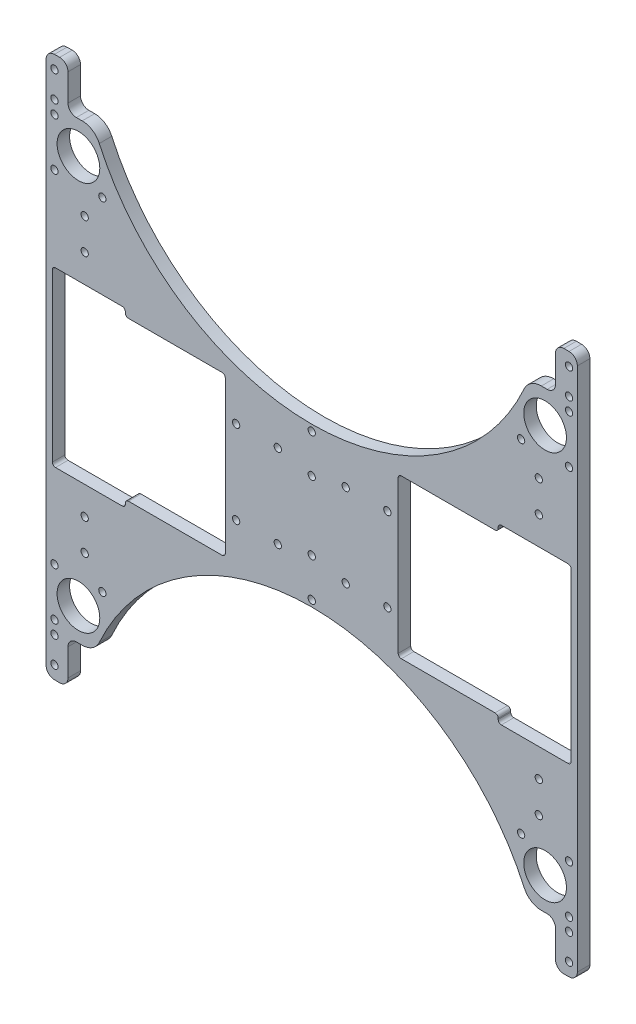
SolidWorks part; units mm, degrees
ref_plane "Plan de face" through (0, 0, 0) normal (0, 0, 1) x (1, 0, 0)
ref_plane "Plan de dessus" through (0, 0, 0) normal (0, 1, 0) x (1, 0, 0)
ref_plane "Plan de droite" through (0, 0, 0) normal (1, 0, 0) x (0, 0, -1)
sketch "Esquisse1" plane through (0, 0, 0) normal (0, 0, 1) x (1, 0, 0)
  line L0 (-109, -55) -> (-109, 55) construction
  line L1 (-16.3, -20) -> (-36.3, -20) construction
  line L2 (-16.3, -20) -> (-16.3, 20) construction
  line L5 (-16.3, 20) -> (-36.3, 20) construction
  line L7 (-36.3, -20) -> (-36.3, 20) construction
  line L8 (-5, 0) -> (-85.5, 0) construction
  line L11 (-41.5, 23) -> (-85.5, 23) construction
  line L13 (-41.5, 38) -> (-89.5, 38)
  line L14 (-41.5, 38) -> (-41.5, -38)
  line L17 (-41.5, -38) -> (-89.5, -38)
  line L19 (-89.5, 38) -> (-89.5, -38) construction
  line L20 (0, 0) -> (-5, 0) construction
  line L21 (0, -23) -> (0, 23) construction
  line L24 (-109, 0) -> (-107, 0) construction
  line L30 (-89.5, -41.5) -> (-89.5, -38)
  line L35 (-89.5, -41.5) -> (-124.5, -41.5)
  line L36 (-89.5, -41.5) -> (-89.5, 41.5) construction
  line L38 (-89.5, 41.5) -> (-124.5, 41.5)
  line L46 (-124.5, -41.5) -> (-124.5, 41.5)
  line L47 (-107, -41.5) -> (-107, 41.5) construction
  line L53 (-89.5, 38) -> (-89.5, 41.5)
  line L55 (-11.3, -23) -> (-76, -23) construction
  line L61 (-11.3, -23) -> (-11.3, 23) construction
  line L62 (-11.3, 23) -> (-76, 23) construction
  line L65 (-76, -23) -> (-76, 23) construction
  line L75 (-41.5, -38) -> (41.5, -38) construction
  line L76 (127.5, -130) -> (127.5, 130)
  line L77 (-127.5, -130) -> (-127.5, 130)
  line L78 (-110.1998, -130) -> (-127.5, -130)
  line L79 (127.5, -130) -> (110.1998, -130)
  line L87 (89.5, 38) -> (89.5, 41.5)
  line L88 (124.5, -41.5) -> (124.5, 41.5)
  line L89 (89.5, 41.5) -> (124.5, 41.5)
  line L90 (89.5, -41.5) -> (124.5, -41.5)
  line L91 (89.5, -41.5) -> (89.5, -38)
  line L92 (41.5, -38) -> (89.5, -38)
  line L93 (41.5, 38) -> (41.5, -38)
  line L94 (41.5, 38) -> (89.5, 38)
  line L95 (-110.1998, 130) -> (-127.5, 130)
  line L96 (127.5, 130) -> (110.1998, 130)
  line L97 (127.5, 0) -> (124.5, 0) construction
  line L98 (-109, 55) -> (-109, 70) construction
  line L99 (-123.5, 93.5) -> (-127.5, 93.5) construction
  line L100 (-123.5, 105) -> (-100.5, 105) construction
  line L101 (-123.5, 105) -> (-123.5, 82) construction
  line L102 (-123.5, 82) -> (-100.5, 82) construction
  line L103 (-100.5, 105) -> (-100.5, 82) construction
  line L104 (-112, 105) -> (-112, 130) construction
  line L105 (-123.5, 123.75) -> (-123.5, 130) construction
  line L106 (-123.5, 105) -> (-123.5, 111.25) construction
  line L107 (-123.5, 111.25) -> (-123.5, 123.75) construction
  line L108 (-117, 109) -> (-117, 130)
  line L109 (110.1998, 109) -> (117, 109)
  line L110 (110.1998, 109) -> (110.1998, 130)
  line L111 (110.1998, 130) -> (117, 130)
  line L112 (117, 109) -> (117, 130)
  line L113 (-110.1998, 109) -> (-117, 109)
  line L114 (-110.1998, 109) -> (-110.1998, 130)
  line L115 (117, -109) -> (117, -130)
  line L116 (110.1998, -109) -> (110.1998, -130)
  line L117 (110.1998, -109) -> (117, -109)
  line L118 (-110.1998, -109) -> (-117, -109)
  line L119 (-110.1998, -109) -> (-110.1998, -130)
  line L120 (-117, -109) -> (-117, -130)
  line L121 (0, -38) -> (0, -35) construction
  line L122 (0, -35) -> (0, -16.5) construction
  circle A53 centre (-16.3, 20) radius 1.75
  circle A54 centre (-36.3, 20) radius 1.75
  circle A55 centre (-36.3, -20) radius 1.75
  circle A56 centre (-16.3, -20) radius 1.75
  circle A57 centre (16.3, -20) radius 1.75
  circle A58 centre (36.3, -20) radius 1.75
  circle A59 centre (36.3, 20) radius 1.75
  circle A60 centre (16.3, 20) radius 1.75
  arc A61 (-110.1998, -130) -> (110.1998, -130) centre (0, -150) cw
  arc A62 (-110.1998, 130) -> (110.1998, 130) centre (0, 150) ccw
  circle A66 centre (-109, 55) radius 1.75
  circle A67 centre (-109, -55) radius 1.75
  circle A68 centre (109, 55) radius 1.75
  circle A69 centre (109, -55) radius 1.75
  circle A70 centre (-109, 70) radius 1.75
  circle A71 centre (-109, -70) radius 1.75
  circle A72 centre (109, -70) radius 1.75
  circle A73 centre (109, 70) radius 1.75
  circle A74 centre (-112, 93.5) radius 10.25
  circle A75 centre (-100.5, 82) radius 1.75
  circle A76 centre (-123.5, 82) radius 1.75
  circle A77 centre (-123.5, 105) radius 1.75
  circle A78 centre (123.5, 105) radius 1.75
  circle A79 centre (100.5, 82) radius 1.75
  circle A80 centre (123.5, 82) radius 1.75
  circle A81 centre (112, 93.5) radius 10.25
  circle A82 centre (100.5, -82) radius 1.75
  circle A83 centre (123.5, -82) radius 1.75
  circle A84 centre (123.5, -105) radius 1.75
  circle A85 centre (112, -93.5) radius 10.25
  circle A86 centre (-123.5, -105) radius 1.75
  circle A87 centre (-123.5, -82) radius 1.75
  circle A88 centre (-100.5, -82) radius 1.75
  circle A89 centre (-112, -93.5) radius 10.25
  circle A98 centre (-123.5, 123.75) radius 1.75
  circle A99 centre (-123.5, 111.25) radius 1.75
  circle A100 centre (123.5, 123.75) radius 1.75
  circle A101 centre (123.5, 111.25) radius 1.75
  circle A102 centre (123.5, -123.75) radius 1.75
  circle A103 centre (123.5, -111.25) radius 1.75
  circle A104 centre (-123.5, -123.75) radius 1.75
  circle A105 centre (-123.5, -111.25) radius 1.75
  arc A106 (-110.1998, 109) -> (-101.9853, 103.7075) centre (-110.1998, 99.9789) cw
  arc A107 (110.1998, 109) -> (101.9853, 103.7075) centre (110.1998, 99.9789) ccw
  arc A108 (110.1998, -109) -> (101.9853, -103.7075) centre (110.1998, -99.9789) cw
  arc A109 (-110.1998, -109) -> (-101.9853, -103.7075) centre (-110.1998, -99.9789) ccw
  circle A110 centre (0, -16.5) radius 1.75
  circle A111 centre (0, -35) radius 1.75
  circle A112 centre (0, 35) radius 1.75
  circle A113 centre (0, 16.5) radius 1.75
  point P0 (-124.5, 0)
  point P13 (-109, 0)
  point P19 (-89.5, 0)
  point P27 (-76, 0)
  point P28 (-41.5, 0)
  point P29 (-36.3, 0)
  point P30 (-16.3, 0)
  point P31 (-11.3, 0)
  point P38 (0, 0)
  point P55 (-127.5, 0)
  point P70 (127.5, 0)
  point P88 (-112, 105)
  point P89 (-123.5, 93.5)
  dimension "D8" = 40
  dimension "D11" = 5
  dimension "D19" = 260
  dimension "D21" = 23
  dimension "D16" = 3.5
  dimension "D17" = 112
  dimension "D20" = 20.5
  dimension "D18" = 12
  dimension "D22" = 25
  dimension "D25" = 12.5
  dimension "D26" = 18.5
  dimension "D29" = 3
  dimension "D1" = 20
  dimension "D2" = 110
  dimension "D3" = 2
  dimension "D4" = 35
  dimension "D5" = 83
  dimension "D6" = 76
  dimension "D7" = 48
  dimension "D9" = 64.7
  dimension "D10" = 46
  dimension "D12" = 13.5
  dimension "D13" = 44
  dimension "D14" = 80.5
  dimension "D15" = 5
  dimension "D23" = 3
  dimension "D24" = 4
  dimension "D27" = 21
  dimension "D28" = 10.5
extrude "Boss.-Extru.1" add sketch "Esquisse1" along normal blind 6 contours A62 L114 L113 L108 L95 L77 L78 L120 L118 L119 A61 L116 L117 L115 L79 L76 L96 L112 L109 L110 A104 A103 A102 A100 A99 A98 A88 A86 A85 A84 A83 A82 A80 A78 A77
fillet "Congé1" radius 4 12 edges at (-127.5, -130, 3) (127.5, -130, 3) (127.5, 130, 3) (-127.5, 130, 3) (117, -109, 3) (117, -130, 3) (-117, -130, 3) (-117, -109, 3) (117, 109, 3) (-117, 109, 3) (-117, 130, 3) (117, 130, 3)
fillet "Congé2" radius 1.5 16 edges at (-89.5, 41.5, 3) (-89.5, 38, 3) (-89.5, -41.5, 3) (-89.5, -38, 3) (89.5, -41.5, 3) (89.5, -38, 3) (89.5, 41.5, 3) (89.5, 38, 3) (41.5, -38, 3) (41.5, 38, 3) (124.5, -41.5, 3) (124.5, 41.5, 3) (-41.5, -38, 3) (-41.5, 38, 3) (-124.5, -41.5, 3) (-124.5, 41.5, 3)
